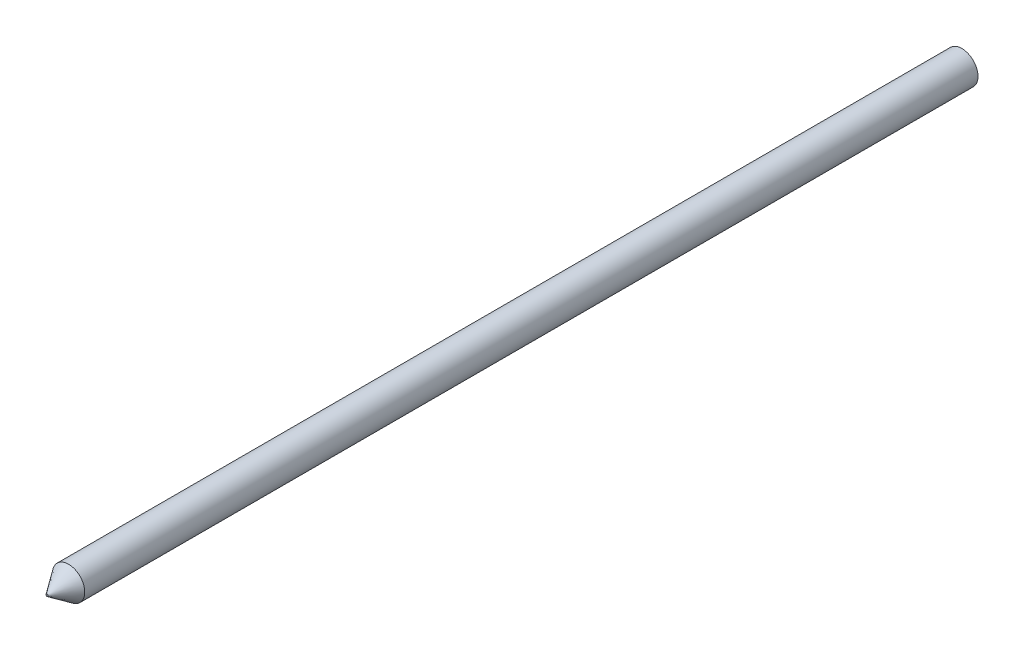
SolidWorks part; units mm, degrees
ref_plane "Přední rovina" through (0, 0, 0) normal (0, 0, 1) x (1, 0, 0)
ref_plane "Horní rovina" through (0, 0, 0) normal (0, 1, 0) x (1, 0, 0)
ref_plane "Pravá rovina" through (0, 0, 0) normal (1, 0, 0) x (0, 0, -1)
sketch "Skica1" plane through (0, 0, 0) normal (0, 0, 1) x (1, 0, 0)
  circle A0 centre (0, 0) radius 3
  dimension "D1" = 6
extrude "Vysunout1" add sketch "Skica1" along normal blind 170
chamfer "Zkosit1" distance 4 angle 35 1 edges at (3, 0, 170)
sketch "Skica2" plane through (0, 0, 170) normal (0, 0, 1) x (1, 0, 0)
  circle A0 centre (0, 0) radius 0.4128
